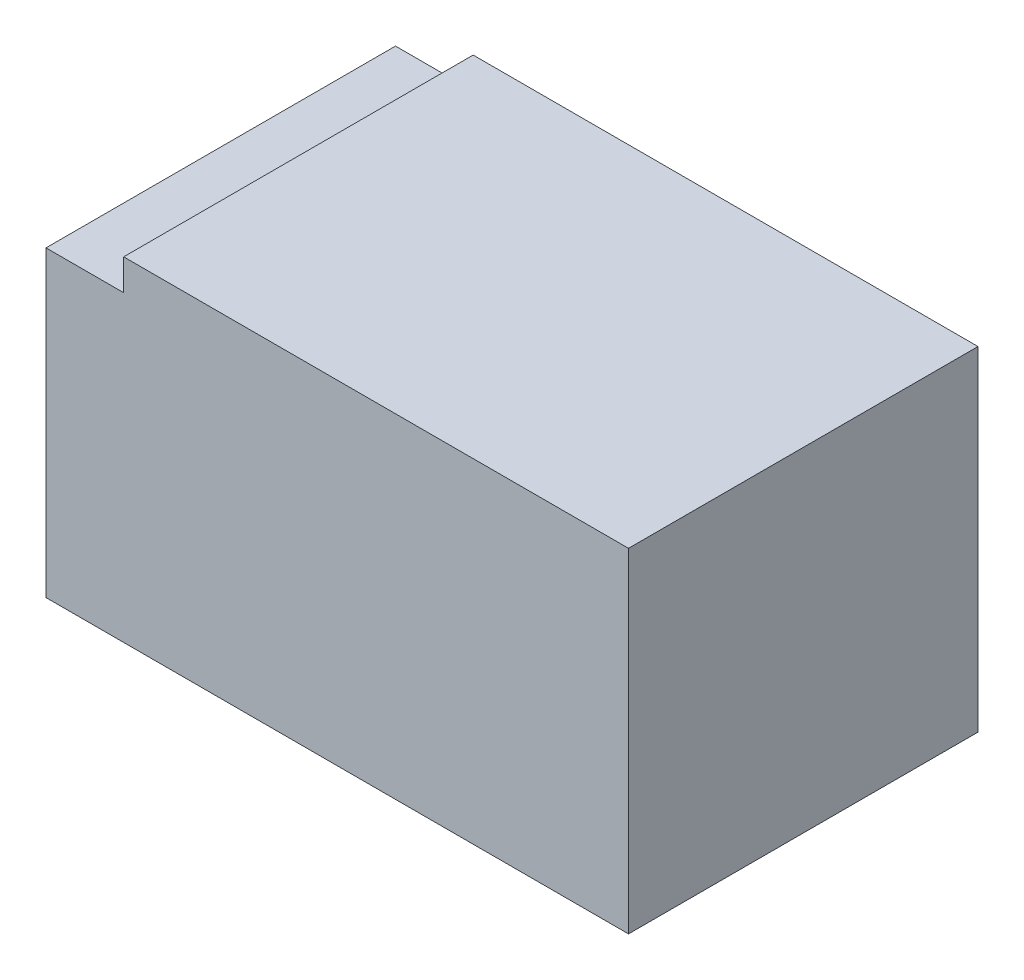
SolidWorks part; units mm, degrees
ref_plane "前视基准面" through (0, 0, 0) normal (0, 0, 1) x (1, 0, 0)
ref_plane "上视基准面" through (0, 0, 0) normal (0, 1, 0) x (1, 0, 0)
ref_plane "右视基准面" through (0, 0, 0) normal (1, 0, 0) x (0, 0, -1)
sketch "草图1" plane through (0, 0, 0) normal (0, 0, 1) x (1, 0, 0)
  line L0 (0, 0) -> (150, 0)
  line L1 (150, 0) -> (150, 86)
  line L2 (150, 86) -> (20, 86)
  line L3 (0, 78) -> (0, 0)
  line L5 (20, 86) -> (20, 78)
  line L6 (20, 78) -> (0, 78)
extrude "凸台-拉伸1" add sketch "草图1" along normal blind 90
